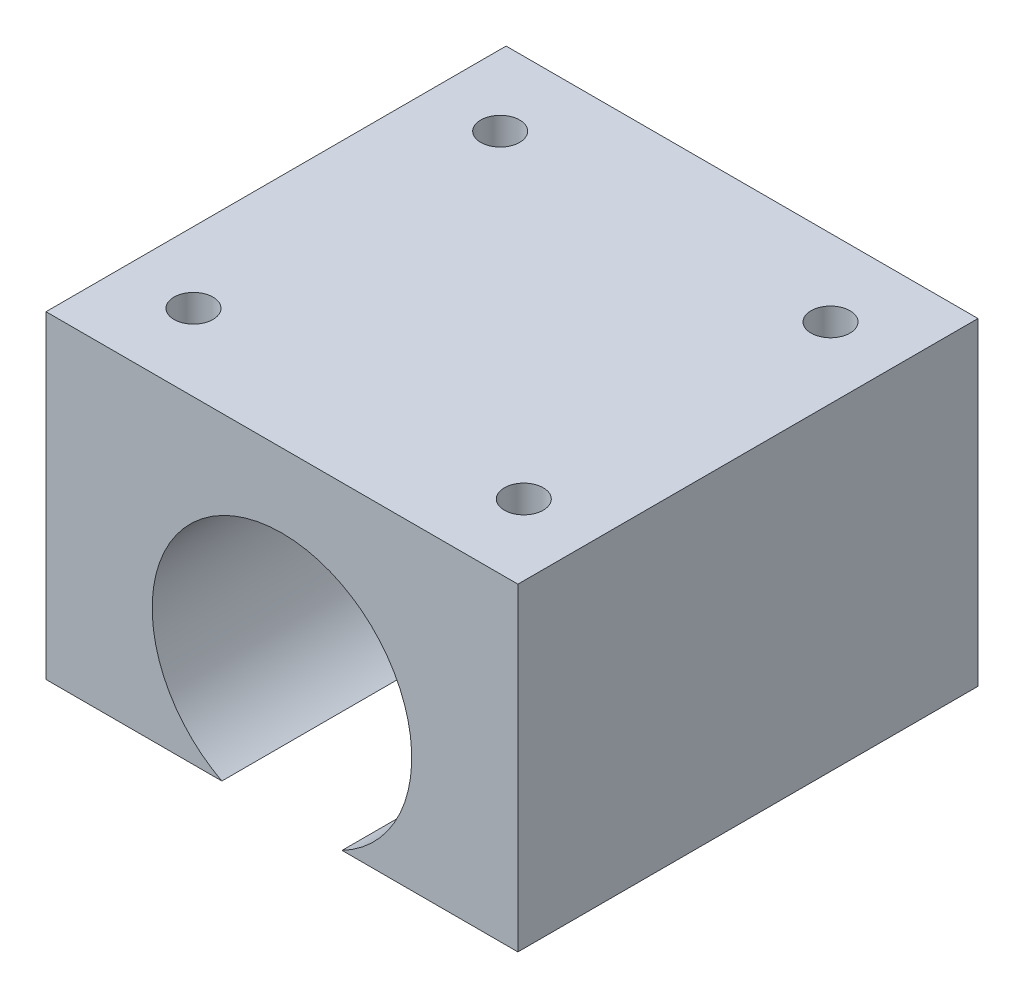
SolidWorks part; units mm, degrees
ref_plane "Front Plane" through (0, 0, 0) normal (0, 0, 1) x (1, 0, 0)
ref_plane "Top Plane" through (0, 0, 0) normal (0, 1, 0) x (1, 0, 0)
ref_plane "Right Plane" through (0, 0, 0) normal (1, 0, 0) x (0, 0, -1)
sketch "Sketch1" plane through (0, 0, 0) normal (0, 0, 1) x (1, 0, 0)
  line L0 (-20, 17.25) -> (20, 17.25)
  line L1 (0, 0) -> (0, 34.5) construction
  line L2 (-20, 17.25) -> (-20, -9.75)
  line L3 (-20, -9.75) -> (-5.0929, -9.75)
  line L4 (20, -9.75) -> (20, 17.25)
  line L5 (5.0929, -9.75) -> (20, -9.75)
  arc A0 (5.0929, -9.75) -> (-5.0929, -9.75) centre (0, 0) ccw
  point P5 (0, 17.25)
  dimension "D1" = 22
  dimension "D2" = 40
  dimension "D3" = 17.25
  dimension "D4" = 27
extrude "Boss-Extrude1" add sketch "Sketch1" along normal blind 39
sketch "Sketch2" plane through (0, 17.25, 0) normal (0, 1, 0) x (1, 0, 0)
  line L0 (0, 0) -> (0, -39) construction
  line L1 (20, -39) -> (-20, -39) construction
  line L2 (-20, -19.5) -> (20, -19.5) construction
  line L3 (-20, -39) -> (-20, 0) construction
  line L4 (20, -39) -> (20, 0) construction
  line L6 (-14, -6.5) -> (14, -6.5) construction
  line L7 (-14, -6.5) -> (-14, -32.5) construction
  line L8 (-14, -32.5) -> (14, -32.5) construction
  line L9 (14, -6.5) -> (14, -32.5) construction
  line L10 (-14, -6.5) -> (14, -32.5) construction
  line L11 (-14, -32.5) -> (14, -6.5) construction
  circle A0 centre (-14, -6.5) radius 1.65
  circle A1 centre (14, -6.5) radius 1.65
  circle A2 centre (-14, -32.5) radius 1.65
  circle A3 centre (14, -32.5) radius 1.65
  point P11 (0, -19.5)
  point P17 (-14, -6.5)
  point P18 (14, -6.5)
  point P19 (14, -32.5)
  point P20 (-14, -32.5)
  dimension "D3" = 3.3
  dimension "D4" = 3.3
  dimension "D5" = 3.3
  dimension "D6" = 3.3
  dimension "D1" = 28
  dimension "D2" = 26
extrude "Cut-Extrude1" cut sketch "Sketch2" against normal blind 5
